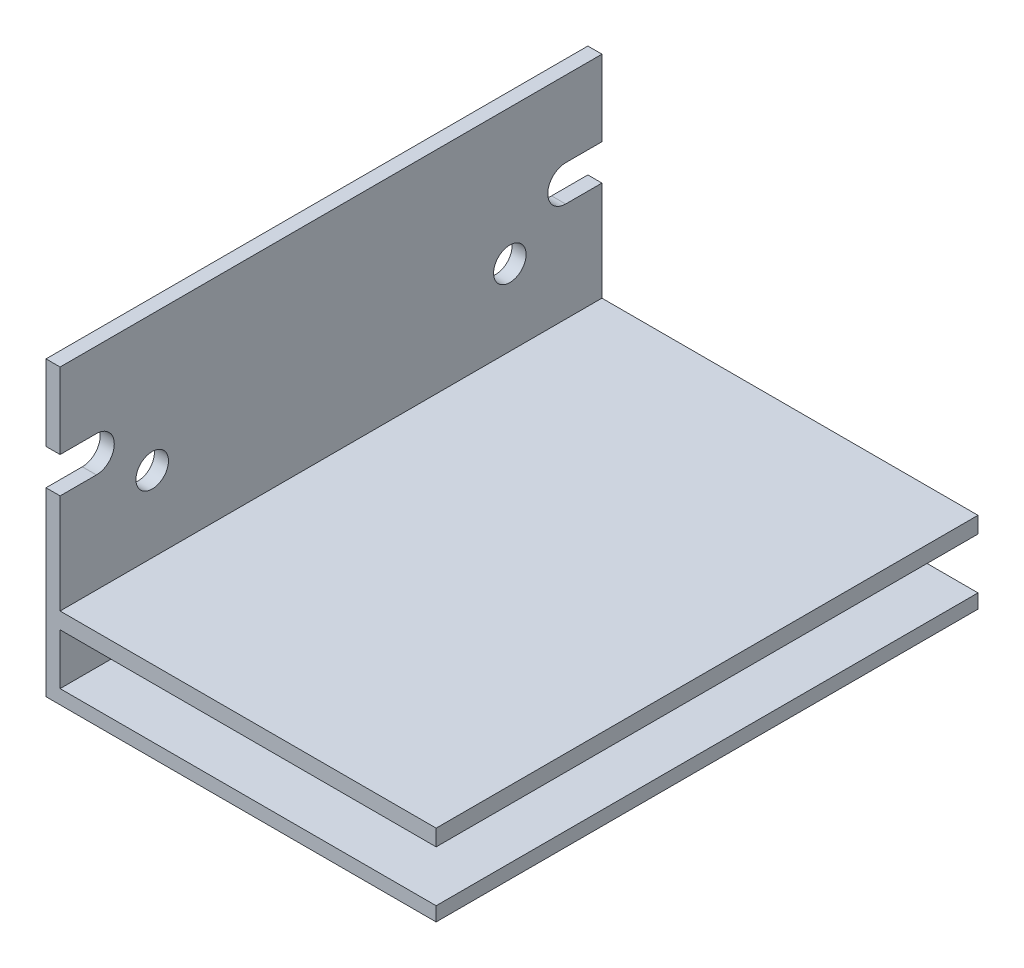
SolidWorks part; units mm, degrees
ref_plane "Plano frontal" through (0, 0, 0) normal (0, 0, 1) x (1, 0, 0)
ref_plane "Plano superior" through (0, 0, 0) normal (0, 1, 0) x (1, 0, 0)
ref_plane "Plano direito" through (0, 0, 0) normal (1, 0, 0) x (0, 0, -1)
sketch "Esboço1" plane through (0, 0, 0) normal (0, 0, 1) x (1, 0, 0)
  line L0 (0, 0) -> (0, 27)
  line L1 (0, 27) -> (1.3, 27)
  line L2 (1.3, 27) -> (1.3, 7.5)
  line L3 (1.3, 1.3) -> (36, 1.3)
  line L4 (36, 1.3) -> (36, 0)
  line L5 (36, 0) -> (0, 0)
  line L6 (36, 6) -> (1.3, 6)
  line L7 (36, 6) -> (36, 7.5)
  line L8 (36, 7.5) -> (1.3, 7.5)
  line L9 (1.3, 6) -> (1.3, 1.3)
  dimension "D1" = 1.3
  dimension "D2" = 36
  dimension "D3" = 27
  dimension "D4" = 1.5
  dimension "D5" = 7.5
extrude "Ressalto-extrusão1" add sketch "Esboço1" along normal blind 50
sketch "Esboço2" plane through (0, 0, 0) normal (-1, 0, 0) x (0, 0, 1)
  line L0 (0, 20) -> (3.35, 20)
  line L1 (0, 27) -> (0, 0) construction
  line L2 (3.35, 16.7) -> (0, 16.7)
  line L3 (0, 16.7) -> (0, 20)
  line L4 (25, 27) -> (25, 0) construction
  line L5 (50, 27) -> (0, 27) construction
  line L6 (50, 0) -> (0, 0) construction
  line L7 (50, 16.7) -> (50, 20)
  line L8 (46.65, 16.7) -> (50, 16.7)
  line L9 (50, 20) -> (46.65, 20)
  arc A0 (3.35, 20) -> (3.35, 16.7) centre (3.35, 18.35) cw
  circle A1 centre (8.5, 14.5) radius 1.5
  circle A2 centre (41.5, 14.5) radius 1.5
  arc A3 (46.65, 20) -> (46.65, 16.7) centre (46.65, 18.35) ccw
  dimension "D3" = 5
  dimension "D5" = 3
  dimension "D1" = 7
  dimension "D2" = 16.7
  dimension "D4" = 8.5
  dimension "D6" = 12.5
extrude "Corte-extrusão1" cut sketch "Esboço2" against normal blind 50
